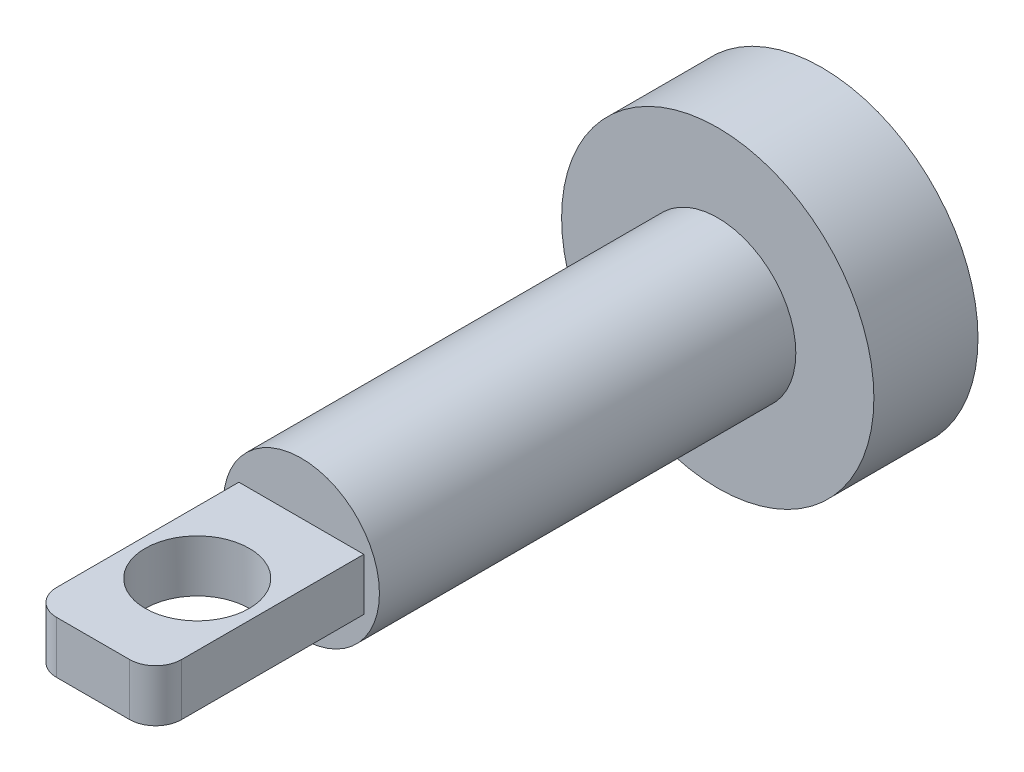
SolidWorks part; units mm, degrees
ref_plane "Front Plane" through (0, 0, 0) normal (0, 0, 1) x (1, 0, 0)
ref_plane "Top Plane" through (0, 0, 0) normal (0, 1, 0) x (1, 0, 0)
ref_plane "Right Plane" through (0, 0, 0) normal (1, 0, 0) x (0, 0, -1)
sketch "Sketch2" plane through (0, 0, 0) normal (0, 0, 1) x (1, 0, 0)
  circle A0 centre (0, 0) radius 38.1
  dimension "D1" = 76.2
extrude "Boss-Extrude1" add sketch "Sketch2" along normal mid plane 25.4
sketch "Sketch3" plane through (0, 0, 12.7) normal (0, 0, 1) x (1, 0, 0)
  circle A0 centre (0, 0) radius 19.05
  dimension "D1" = 38.1
extrude "Boss-Extrude2" add sketch "Sketch3" along normal blind 101.6
sketch "Sketch4" plane through (0, 0, 114.3) normal (0, 0, 1) x (1, 0, 0)
  line L1 (-15.24, 6.35) -> (15.24, 6.35)
  line L2 (-15.24, 6.35) -> (-15.24, -6.35)
  line L3 (-15.24, -6.35) -> (15.24, -6.35)
  line L4 (15.24, 6.35) -> (15.24, -6.35)
  line L5 (-15.24, 6.35) -> (15.24, -6.35) construction
  line L6 (-15.24, -6.35) -> (15.24, 6.35) construction
  point P0 (0, 0)
  dimension "D1" = 12.7
  dimension "D2" = 30.48
extrude "Boss-Extrude3" add sketch "Sketch4" along normal blind 50.8
fillet "Fillet1" radius 6.35 2 edges at (-15.24, 0, 165.1) (15.24, 0, 165.1)
sketch "Sketch5" plane through (0, 6.35, 0) normal (0, 1, 0) x (1, 0, 0)
  line L0 (8.89, -165.1) -> (-8.89, -165.1) construction
  circle A0 centre (0, -139.7) radius 12.7
  dimension "D1" = 25.4
  dimension "D2" = 25.4
extrude "Cut-Extrude1" cut sketch "Sketch5" against normal through all both and the other way through all
